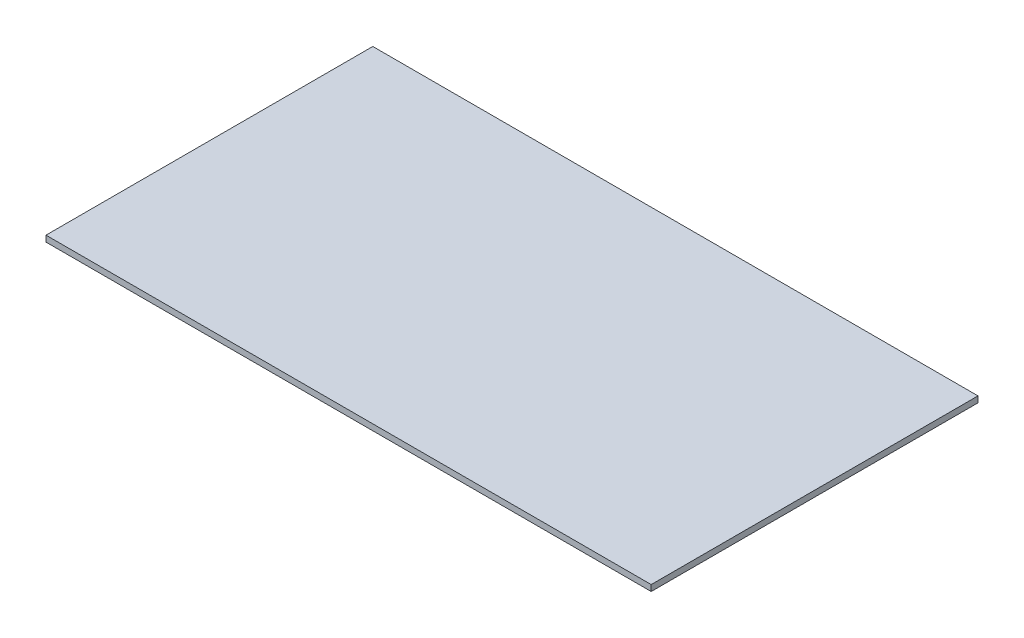
SolidWorks part; units mm, degrees
ref_plane "Front Plane" through (0, 0, 0) normal (0, 0, 1) x (1, 0, 0)
ref_plane "Top Plane" through (0, 0, 0) normal (0, 1, 0) x (1, 0, 0)
ref_plane "Right Plane" through (0, 0, 0) normal (1, 0, 0) x (0, 0, -1)
sketch "Sketch1" plane through (0, 0, 0) normal (0, 1, 0) x (1, 0, 0)
  line L1 (-500, -270) -> (500, -270)
  line L2 (-500, -270) -> (-500, 270)
  line L3 (-500, 270) -> (500, 270)
  line L4 (500, -270) -> (500, 270)
  line L5 (-500, -270) -> (500, 270) construction
  line L6 (-500, 270) -> (500, -270) construction
  point P0 (0, 0)
  dimension "D1" = 540
  dimension "D2" = 1000
extrude "Boss-Extrude1" add sketch "Sketch1" along normal blind 10
